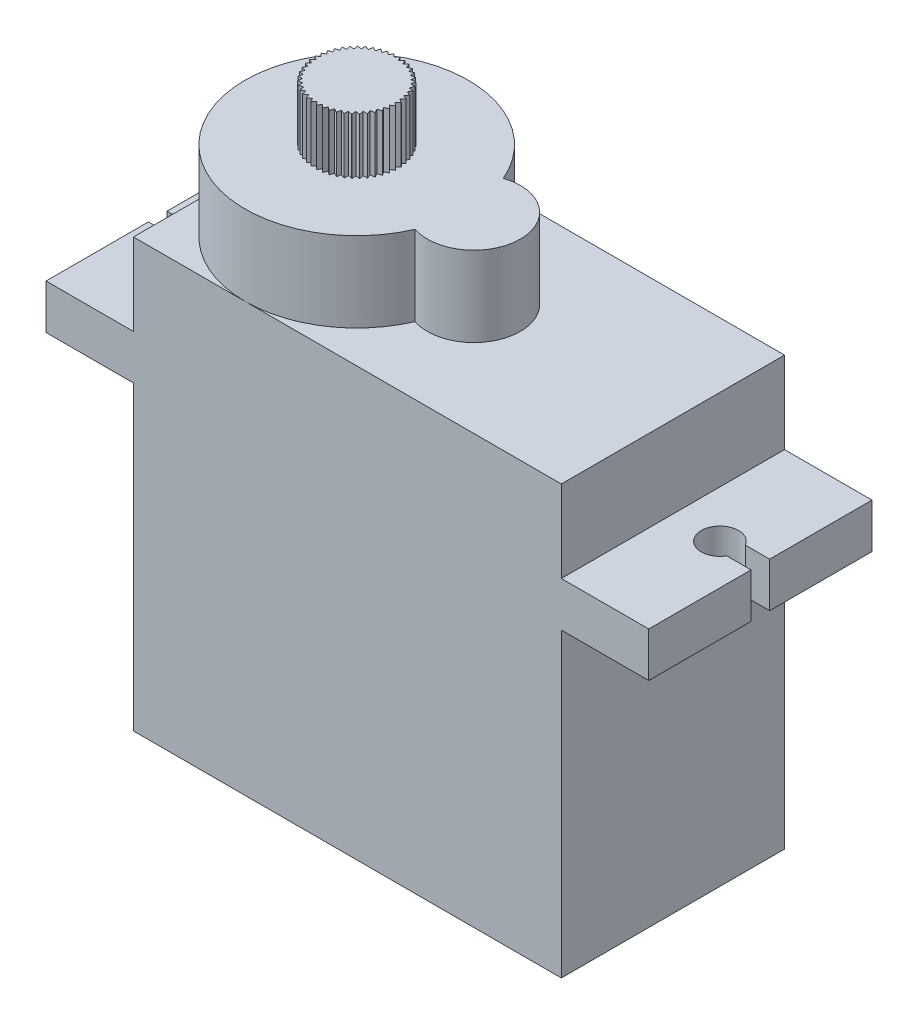
SolidWorks part; units mm, degrees
ref_plane "Front Plane" through (0, 0, 0) normal (0, 0, 1) x (1, 0, 0)
ref_plane "Top Plane" through (0, 0, 0) normal (0, 1, 0) x (1, 0, 0)
ref_plane "Right Plane" through (0, 0, 0) normal (1, 0, 0) x (0, 0, -1)
sketch "Sketch2" plane through (0, 0, 0) normal (0, 1, 0) x (1, 0, 0)
  line L1 (-11.5, -6) -> (11.5, -6)
  line L2 (-11.5, -6) -> (-11.5, 6)
  line L3 (-11.5, 6) -> (11.5, 6)
  line L4 (11.5, -6) -> (11.5, 6)
  line L5 (-11.5, -6) -> (11.5, 6) construction
  line L6 (-11.5, 6) -> (11.5, -6) construction
  point P0 (0, 0)
  dimension "D1" = 12
  dimension "D2" = 23
extrude "Boss-Extrude1" add sketch "Sketch2" against normal blind 23
sketch "Sketch3" plane through (0, 0, 0) normal (0, 1, 0) x (1, 0, 0)
  line L0 (11.5, 6) -> (-11.5, 6) construction
  line L1 (-16.2, -6) -> (16.2, -6)
  line L2 (-16.2, -6) -> (-16.2, 6)
  line L3 (-16.2, 6) -> (16.2, 6)
  line L4 (16.2, -6) -> (16.2, 6)
  line L5 (-16.2, -6) -> (16.2, 6) construction
  line L6 (-16.2, 6) -> (16.2, -6) construction
  line L8 (-15.5843, 0.5) -> (-16.2, 0.5)
  line L9 (-15.5843, 0.5) -> (-15.5843, -0.5)
  line L10 (-15.5843, -0.5) -> (-16.2, -0.5)
  line L11 (-16.2, 0.5) -> (-16.2, -0.5)
  line L12 (16.2, 0.5) -> (14.8944, 0.5)
  line L13 (16.2, 0.5) -> (16.2, -0.5)
  line L14 (16.2, -0.5) -> (14.8944, -0.5)
  line L15 (14.8944, 0.5) -> (14.8944, -0.5)
  circle A0 centre (-14.7183, 0) radius 1
  circle A1 centre (14.0284, 0) radius 1
  point P0 (0, 0)
  point P12 (0, 0)
  line M15 (11.5, -6) -> (11.5, 6)
  line M17 (-11.5, 6) -> (-11.5, -6)
  dimension "D2" = 2
  dimension "D1" = 32.4
  dimension "D3" = 1
  dimension "D4" = 1
extrude "Boss-Extrude2" add sketch "Sketch3" against normal blind 2.4 from offset 4.4 contours A0 L10 L2 L1 L3 L8 M17 | A1 L12 L4 L3 L1 L14 M15 offset against normal yes
sketch "Sketch4" plane through (0, 0, 0) normal (0, 1, 0) x (1, 0, 0)
  line L0 (-11.5, 6) -> (-11.5, -6) construction
  line L1 (11.5, 6) -> (-11.5, 6) construction
  line L2 (3.3, 0) -> (-11.5, 0) construction
  circle A0 centre (-5.5, 0) radius 6
  circle A1 centre (0.8, 0) radius 2.5
  dimension "D1" = 14.8
  dimension "D2" = 5
extrude "Boss-Extrude3" add sketch "Sketch4" along normal blind 4.3 contours L2 A1 A0 | A1 L2 A0 | A1 L2 A0 | L2 A1 A0 | L2 A0 A1 | A0 L2 A1
sketch "Sketch5" plane through (0, 4.3, 0) normal (0, 1, 0) x (1, 0, 0)
  line L0 (-3.255, -0.15) -> (-3.4372, 0)
  line L1 (-3.4372, 0) -> (-3.255, 0.15)
  line L2 (-3.295, -0.4479) -> (-3.4556, -0.2749)
  line L3 (-3.4556, -0.2749) -> (-3.255, -0.1506)
  line L4 (-3.3744, -0.7378) -> (-3.5105, -0.545)
  line L5 (-3.5105, -0.545) -> (-3.2951, -0.4484)
  line L6 (-3.4917, -1.0145) -> (-3.6009, -0.8053)
  line L7 (-3.6009, -0.8053) -> (-3.3746, -0.7383)
  line L8 (-3.6448, -1.2731) -> (-3.7252, -1.0512)
  line L9 (-3.7252, -1.0512) -> (-3.492, -1.015)
  line L10 (-3.8311, -1.5091) -> (-3.8811, -1.2784)
  line L11 (-3.8811, -1.2784) -> (-3.6452, -1.2736)
  line L12 (-4.0471, -1.718) -> (-4.0659, -1.4828)
  line L13 (-4.0659, -1.4828) -> (-3.8315, -1.5095)
  line L14 (-4.2891, -1.8964) -> (-4.2764, -1.6607)
  line L15 (-4.2764, -1.6607) -> (-4.0476, -1.7184)
  line L16 (-4.5526, -2.0408) -> (-4.5086, -1.809)
  line L17 (-4.5086, -1.809) -> (-4.2896, -1.8967)
  line L18 (-4.8331, -2.1489) -> (-4.7586, -1.925)
  line L19 (-4.7586, -1.925) -> (-4.5532, -2.0411)
  line L20 (-5.1255, -2.2186) -> (-5.0218, -2.0066)
  line L21 (-5.0218, -2.0066) -> (-4.8337, -2.1491)
  line L22 (-5.4245, -2.2487) -> (-5.2935, -2.0525)
  line L23 (-5.2935, -2.0525) -> (-5.126, -2.2187)
  line L24 (-5.7249, -2.2387) -> (-5.5689, -2.0617)
  line L25 (-5.5689, -2.0617) -> (-5.4251, -2.2488)
  line L26 (-6.0213, -2.1888) -> (-5.8431, -2.0341)
  line L27 (-5.8431, -2.0341) -> (-5.7255, -2.2387)
  line L28 (-6.3084, -2.0998) -> (-6.1112, -1.9702)
  line L29 (-6.1112, -1.9702) -> (-6.0219, -2.1886)
  line L30 (-6.5811, -1.9733) -> (-6.3683, -1.8712)
  line L31 (-6.3683, -1.8712) -> (-6.3089, -2.0996)
  line L32 (-6.8344, -1.8116) -> (-6.61, -1.7387)
  line L33 (-6.61, -1.7387) -> (-6.5816, -1.973)
  line L34 (-7.064, -1.6176) -> (-6.8318, -1.5753)
  line L35 (-6.8318, -1.5753) -> (-6.8349, -1.8112)
  line L36 (-7.2656, -1.3947) -> (-7.0299, -1.3837)
  line L37 (-7.0299, -1.3837) -> (-7.0644, -1.6172)
  line L38 (-7.4358, -1.1469) -> (-7.2007, -1.1674)
  line L39 (-7.2007, -1.1674) -> (-7.266, -1.3942)
  line L40 (-7.5714, -0.8786) -> (-7.3411, -0.9304)
  line L41 (-7.3411, -0.9304) -> (-7.436, -1.1464)
  line L42 (-7.67, -0.5947) -> (-7.4487, -0.6767)
  line L43 (-7.4487, -0.6767) -> (-7.5716, -0.8781)
  line L44 (-7.7299, -0.3002) -> (-7.5215, -0.4109)
  line L45 (-7.5215, -0.4109) -> (-7.6701, -0.5942)
  line L46 (-7.75, -0.0003) -> (-7.5582, -0.1378)
  line L47 (-7.5582, -0.1378) -> (-7.73, -0.2996)
  line L48 (-7.73, 0.2996) -> (-7.5582, 0.1378)
  line L49 (-7.5582, 0.1378) -> (-7.75, 0.0003)
  line L50 (-7.6701, 0.5942) -> (-7.5215, 0.4109)
  line L51 (-7.5215, 0.4109) -> (-7.7299, 0.3002)
  line L52 (-7.5716, 0.8781) -> (-7.4487, 0.6767)
  line L53 (-7.4487, 0.6767) -> (-7.67, 0.5947)
  line L54 (-7.436, 1.1464) -> (-7.3411, 0.9304)
  line L55 (-7.3411, 0.9304) -> (-7.5714, 0.8786)
  line L56 (-7.266, 1.3942) -> (-7.2007, 1.1674)
  line L57 (-7.2007, 1.1674) -> (-7.4358, 1.1469)
  line L58 (-7.0644, 1.6172) -> (-7.0299, 1.3837)
  line L59 (-7.0299, 1.3837) -> (-7.2656, 1.3947)
  line L60 (-6.8349, 1.8112) -> (-6.8318, 1.5753)
  line L61 (-6.8318, 1.5753) -> (-7.064, 1.6176)
  line L62 (-6.5816, 1.973) -> (-6.61, 1.7387)
  line L63 (-6.61, 1.7387) -> (-6.8344, 1.8116)
  line L64 (-6.3089, 2.0996) -> (-6.3683, 1.8712)
  line L65 (-6.3683, 1.8712) -> (-6.5811, 1.9733)
  line L66 (-6.0219, 2.1886) -> (-6.1112, 1.9702)
  line L67 (-6.1112, 1.9702) -> (-6.3084, 2.0998)
  line L68 (-5.7255, 2.2387) -> (-5.8431, 2.0341)
  line L69 (-5.8431, 2.0341) -> (-6.0213, 2.1888)
  line L70 (-5.4251, 2.2488) -> (-5.5689, 2.0617)
  line L71 (-5.5689, 2.0617) -> (-5.7249, 2.2387)
  line L72 (-5.126, 2.2187) -> (-5.2935, 2.0525)
  line L73 (-5.2935, 2.0525) -> (-5.4245, 2.2487)
  line L74 (-4.8337, 2.1491) -> (-5.0218, 2.0066)
  line L75 (-5.0218, 2.0066) -> (-5.1255, 2.2186)
  line L76 (-4.5532, 2.0411) -> (-4.7586, 1.925)
  line L77 (-4.7586, 1.925) -> (-4.8331, 2.1489)
  line L78 (-4.2896, 1.8967) -> (-4.5086, 1.809)
  line L79 (-4.5086, 1.809) -> (-4.5526, 2.0408)
  line L80 (-4.0476, 1.7184) -> (-4.2764, 1.6607)
  line L81 (-4.2764, 1.6607) -> (-4.2891, 1.8964)
  line L82 (-3.8315, 1.5095) -> (-4.0659, 1.4828)
  line L83 (-4.0659, 1.4828) -> (-4.0471, 1.718)
  line L84 (-3.6452, 1.2736) -> (-3.8811, 1.2784)
  line L85 (-3.8811, 1.2784) -> (-3.8311, 1.5091)
  line L86 (-3.492, 1.015) -> (-3.7252, 1.0512)
  line L87 (-3.7252, 1.0512) -> (-3.6448, 1.2731)
  line L88 (-3.3746, 0.7383) -> (-3.6009, 0.8053)
  line L89 (-3.6009, 0.8053) -> (-3.4917, 1.0145)
  line L90 (-3.2951, 0.4484) -> (-3.5105, 0.545)
  line L91 (-3.5105, 0.545) -> (-3.3744, 0.7378)
  line L92 (-3.255, 0.1506) -> (-3.4556, 0.2749)
  line L93 (-3.4556, 0.2749) -> (-3.295, 0.4479)
  circle A0 centre (-5.5, 0) radius 2.25
  point P146 (-5.5, 0)
  dimension "D1" = 4.5
  dimension "D2" = 0.15
  dimension "D3" = 47
extrude "Boss-Extrude4" add sketch "Sketch5" along normal blind 3 contours L25 A0 L22 L23 L20 L21 L18 L19 L16 L17 L14 L15 L12 L13 L10 L11 L8 L9 L6 L7 L4 L5 L2 L3 L0 L1 L92 L93 L90 L91 L88 L89 L86 L87 L84
sketch "Sketch6" plane through (-11.5, 0, 0) normal (-1, 0, 0) x (0, 0, 1)
  line L0 (-6, -23) -> (6, -23) construction
  line L1 (-1.5, -17) -> (1.5, -17)
  line L2 (-1.5, -17) -> (-1.5, -18)
  line L3 (-1.5, -18) -> (1.5, -18)
  line L4 (1.5, -17) -> (1.5, -18)
  point P7 (0, -17)
  dimension "D1" = 5
  dimension "D2" = 3
  dimension "D3" = 1
extrude "Boss-Extrude5" add sketch "Sketch6" along normal blind 3
